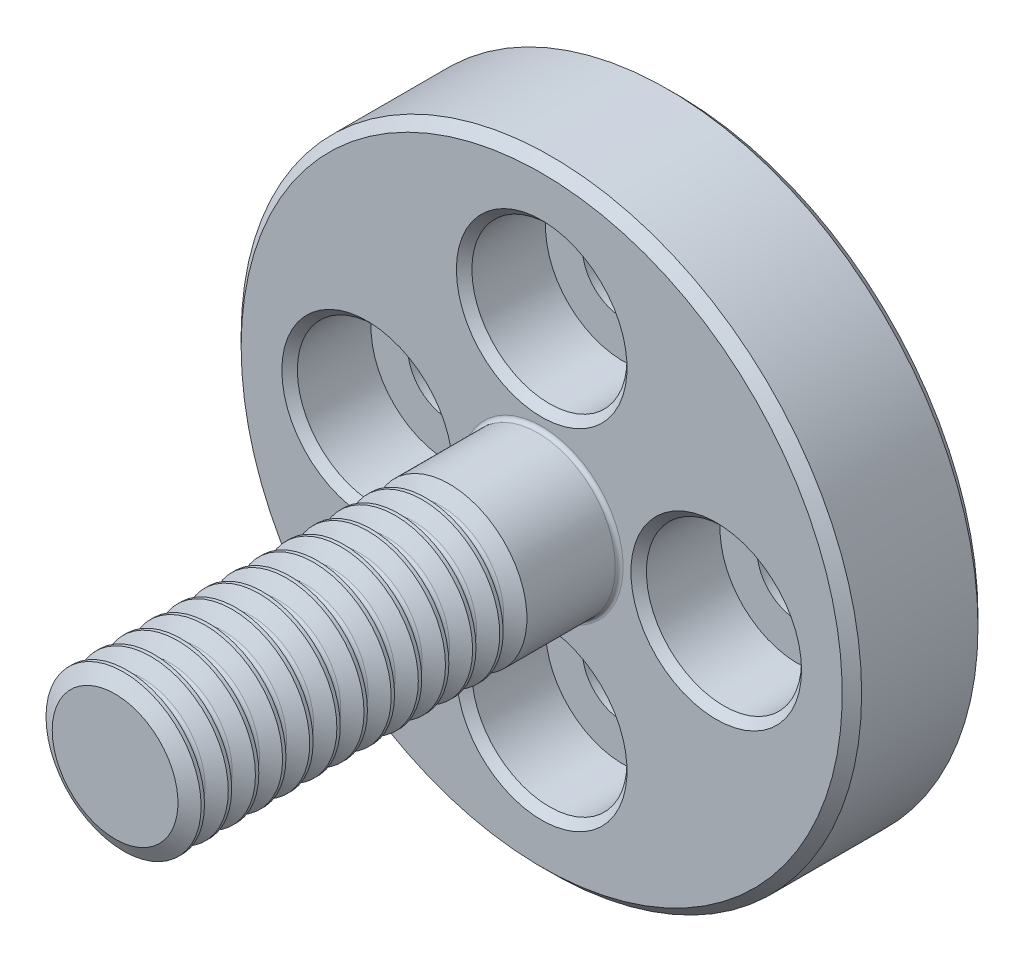
SolidWorks part; units mm, degrees
ref_plane "Plan de face" through (0, 0, 0) normal (0, 0, 1) x (1, 0, 0)
ref_plane "Plan de dessus" through (0, 0, 0) normal (0, 1, 0) x (1, 0, 0)
ref_plane "Plan de droite" through (0, 0, 0) normal (1, 0, 0) x (0, 0, -1)
sketch "Esquisse1" plane through (0, 0, 0) normal (1, 0, 0) x (0, 0, -1)
  line L0 (-1000, 0) -> (49000, 0) construction
  line L1 (0, 0) -> (0, 8)
  line L2 (0, 8) -> (-3.5, 8)
  line L3 (-3.5, 8) -> (-3.5, 2)
  line L4 (-3.5, 2) -> (-14.5, 2)
  line L5 (-14.5, 2) -> (-14.5, 0)
  line L6 (0, 0) -> (-14.5, 0)
  dimension "D1" = 14.5
  dimension "D2" = 2
  dimension "D3" = 8
  dimension "D4" = 11
revolve "Révolution1" add sketch "Esquisse1" angle 360 about L0
hole_wizard "Chambrage pour vis à tête hexagonale M21" positions "Esquisse3" profile "Esquisse2" counterbore size "M2" standard "Iso" end condition through all
sketch "Esquisse3" plane through (0, 0, 3.5) normal (0, 0, 1) x (1, 0, 0)
  point P0 (0, 4.5)
  dimension "D1" = 4.5
sketch "Esquisse2" plane through (0, 4.5, 3.5) normal (1, 0, 0) x (0, -1, 0)
  line L0 (0, 0) -> (0, 3.5)
  line L1 (0, 3.5) -> (1.05, 3.5)
  line L3 (1.05, 3.5) -> (1.05, 2.1)
  line L4 (1.05, 2.1) -> (2, 2.1)
  line L5 (2, 2.1) -> (2, 0)
  line L7 (2, 0) -> (0, 0)
  line L11 (0, -6.35) -> (0, 107.95) construction
  dimension "Diamètre du perçage jusqu'au prochain" = 2.1
  dimension "Profondeur du perçage jusqu'au prochain" = 3.5
  dimension "Diamètre du chambrage" = 4
  dimension "Profondeur du chambrage" = 2.1
pattern_circular "Répétition circulaire1" count 4 over 360 about axis through (0, 0, 0) along (0, 0, 1) of "Chambrage pour vis à tête hexagonale M21"
sketch "Esquisse4" plane through (0, 0, 0) normal (0, 0, -1) x (-1, 0, 0)
  circle A0 centre (0, 0) radius 1
  dimension "D1" = 2
extrude "Enlèv. mat.-Extru.1" cut sketch "Esquisse4" against normal blind 3.5
sketch "Esquisse13" plane through (0, 0, 0) normal (1, 0, 0) x (0, 0, -1)
  line L0 (-14.2375, 2.0758) -> (-14.9375, 2.0758)
  line L1 (-14.9375, 2.0758) -> (-14.5875, 1.4696)
  line L2 (-14.5875, 1.4696) -> (-14.2375, 2.0758)
  line L3 (-14.5875, 2.0758) -> (-14.5875, 1.4696) construction
  line L5 (-14.5, 2) -> (-14.5, -2) construction
  line L6 (-14.675, 1.6211) -> (-14.5, 1.6211)
  line L7 (-3.5, 0) -> (-14.5, 0) construction
  arc A0 (-14.675, 1.6211) -> (-14.5, 1.6211) centre (-14.5875, 1.6716) ccw
  dimension "D1" = 0.7
  dimension "D2" = 60.001
  dimension "D3" = 1.6211
  dimension "D4" = 0.1515
revolve "Enlèvement de matière-Révolution1" cut sketch "Esquisse13" angle 360 about axis through (0, 0, 1000) along (0, 0, 1)
pattern_linear "Répétition linéaire1" count 13 spacing 0.7 along (0, 0, -1) of "Enlèvement de matière-Révolution1"
chamfer "Chanfrein1" distance 0.2 angle 45 4 edges at (6.5, 0, 3.5) (2, -4.5, 3.5) (-2.5, 0, 3.5) (2, 4.5, 3.5)
chamfer "Chanfrein2" distance 0.25 angle 45 2 edges at (8, 0, 0) (8, 0, 3.5)
fillet "Congé2" radius 0.1 1 edges at (2, 0, 3.5)
